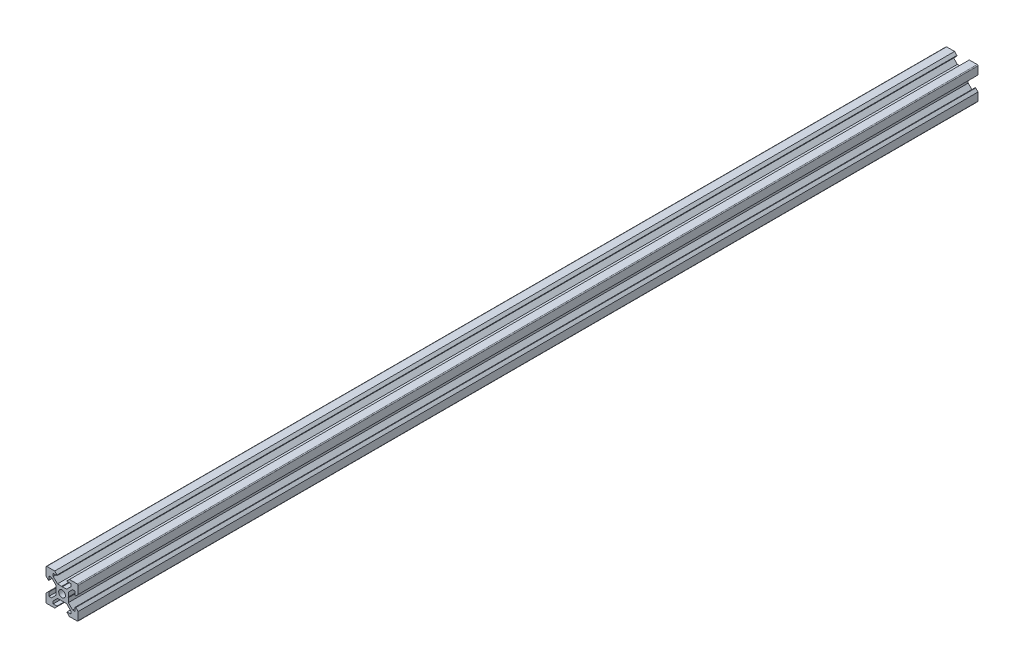
SolidWorks part; units mm, degrees
material "6061-T6 (SS)"
ref_plane "Front Plane" through (0, 0, 0) normal (0, 0, 1) x (1, 0, 0)
ref_plane "Top Plane" through (0, 0, 0) normal (0, 1, 0) x (1, 0, 0)
ref_plane "Right Plane" through (0, 0, 0) normal (1, 0, 0) x (0, 0, -1)
sketch "Sketch1" plane through (0, 0, 0) normal (0, 0, 1) x (1, 0, 0)
  line L1 (9.5, -10) -> (-9.5, -10)
  line L2 (10, -9.5) -> (10, 9.5)
  line L3 (9.5, 10) -> (-9.5, 10)
  line L4 (-10, -9.5) -> (-10, 9.5)
  line L5 (10, -10) -> (-10, 10) construction
  line L6 (10, 10) -> (-10, -10) construction
  circle A0 centre (0, 0) radius 2.1
  arc A1 (-9.5, 10) -> (-10, 9.5) centre (-9.5, 9.5) ccw
  arc A2 (10, 9.5) -> (9.5, 10) centre (9.5, 9.5) ccw
  arc A3 (9.5, -10) -> (10, -9.5) centre (9.5, -9.5) ccw
  arc A4 (-9.5, -10) -> (-10, -9.5) centre (-9.5, -9.5) cw
  point P0 (0, 0)
  line B0 (0, 0) -> (0, 10) construction
  line B1 (0, 3.69) -> (-0.21, 3.9)
  line B2 (-0.21, 3.9) -> (-2.8393, 3.9)
  line B3 (-2.8393, 3.9) -> (-5.5, 6.5607)
  line B4 (-5.5, 6.5607) -> (-5.5, 8.2)
  line B5 (-5.5, 8.2) -> (-3.125, 8.2)
  line B6 (-3.125, 8.2) -> (-3.125, 8.545)
  line B7 (-3.125, 8.545) -> (-4.58, 10)
  line B8 (-4.58, 10) -> (4.58, 10)
  line B9 (0, 0) -> (-5.9132, 5.9132) construction
  line B10 (3.125, 8.545) -> (4.58, 10)
  line B11 (3.125, 8.2) -> (3.125, 8.545)
  line B12 (5.5, 8.2) -> (3.125, 8.2)
  line B13 (5.5, 6.5607) -> (5.5, 8.2)
  line B14 (2.8393, 3.9) -> (5.5, 6.5607)
  line B15 (0.21, 3.9) -> (2.8393, 3.9)
  line B16 (0, 3.69) -> (0.21, 3.9)
  line B17 (0, 0) -> (-10, 0) construction
  line B18 (-3.69, 0) -> (-3.9, -0.21)
  line B19 (-3.9, -0.21) -> (-3.9, -2.8393)
  line B20 (-3.9, -2.8393) -> (-6.5607, -5.5)
  line B21 (-6.5607, -5.5) -> (-8.2, -5.5)
  line B22 (-8.2, -5.5) -> (-8.2, -3.125)
  line B23 (-8.2, -3.125) -> (-8.545, -3.125)
  line B24 (-8.545, -3.125) -> (-10, -4.58)
  line B25 (-10, -4.58) -> (-10, 4.58)
  line B26 (0, 0) -> (-5.9132, -5.9132) construction
  line B27 (-8.545, 3.125) -> (-10, 4.58)
  line B28 (-8.2, 3.125) -> (-8.545, 3.125)
  line B29 (-8.2, 5.5) -> (-8.2, 3.125)
  line B30 (-6.5607, 5.5) -> (-8.2, 5.5)
  line B31 (-3.9, 2.8393) -> (-6.5607, 5.5)
  line B32 (-3.9, 0.21) -> (-3.9, 2.8393)
  line B33 (-3.69, 0) -> (-3.9, 0.21)
  line B34 (0, 0) -> (0, -10) construction
  line B35 (0, -3.69) -> (0.21, -3.9)
  line B36 (0.21, -3.9) -> (2.8393, -3.9)
  line B37 (2.8393, -3.9) -> (5.5, -6.5607)
  line B38 (5.5, -6.5607) -> (5.5, -8.2)
  line B39 (5.5, -8.2) -> (3.125, -8.2)
  line B40 (3.125, -8.2) -> (3.125, -8.545)
  line B41 (3.125, -8.545) -> (4.58, -10)
  line B42 (4.58, -10) -> (-4.58, -10)
  line B43 (0, 0) -> (5.9132, -5.9132) construction
  line B44 (-3.125, -8.545) -> (-4.58, -10)
  line B45 (-3.125, -8.2) -> (-3.125, -8.545)
  line B46 (-5.5, -8.2) -> (-3.125, -8.2)
  line B47 (-5.5, -6.5607) -> (-5.5, -8.2)
  line B48 (-2.8393, -3.9) -> (-5.5, -6.5607)
  line B49 (-0.21, -3.9) -> (-2.8393, -3.9)
  line B50 (0, -3.69) -> (-0.21, -3.9)
  line B51 (0, 0) -> (10, 0) construction
  line B52 (3.69, 0) -> (3.9, 0.21)
  line B53 (3.9, 0.21) -> (3.9, 2.8393)
  line B54 (3.9, 2.8393) -> (6.5607, 5.5)
  line B55 (6.5607, 5.5) -> (8.2, 5.5)
  line B56 (8.2, 5.5) -> (8.2, 3.125)
  line B57 (8.2, 3.125) -> (8.545, 3.125)
  line B58 (8.545, 3.125) -> (10, 4.58)
  line B59 (10, 4.58) -> (10, -4.58)
  line B60 (0, 0) -> (5.9132, 5.9132) construction
  line B61 (8.545, -3.125) -> (10, -4.58)
  line B62 (8.2, -3.125) -> (8.545, -3.125)
  line B63 (8.2, -5.5) -> (8.2, -3.125)
  line B64 (6.5607, -5.5) -> (8.2, -5.5)
  line B65 (3.9, -2.8393) -> (6.5607, -5.5)
  line B66 (3.9, -0.21) -> (3.9, -2.8393)
  line B67 (3.69, 0) -> (3.9, -0.21)
  dimension "D1" = 4.2
  dimension "D3" = 0.5
  dimension "D2" = 20
sketch_block_instance "V Slot 1-4"
sketch_block "V Slot 1" parameters "D1"=10, "D2"=11, "D3"=4.3, "D4"=1.8, "D5"=0.21, "D6"=45, "D7"=9.16, "D8"=1.5, "D9"=6.25
sketch_block_instance "V Slot 1-5"
sketch_block_instance "V Slot 1-6"
sketch_block_instance "V Slot 1-7"
extrude "Boss-Extrude1" add sketch "Sketch1" along normal blind 560 contours B67 B52 B53 B54 B55 B56 B57 B58 L2 A2 L3 B10 B11 B12 B13 B14 B15 B16 B1 B2 B3 B4 B5 B6 B7 A1 L4 B27 B28 B29 B30 B31 B32 B33 B18 B19 B20 B21 B22 B23 B24 A4 L1 B44 B45 B46 B47 B48 B49
